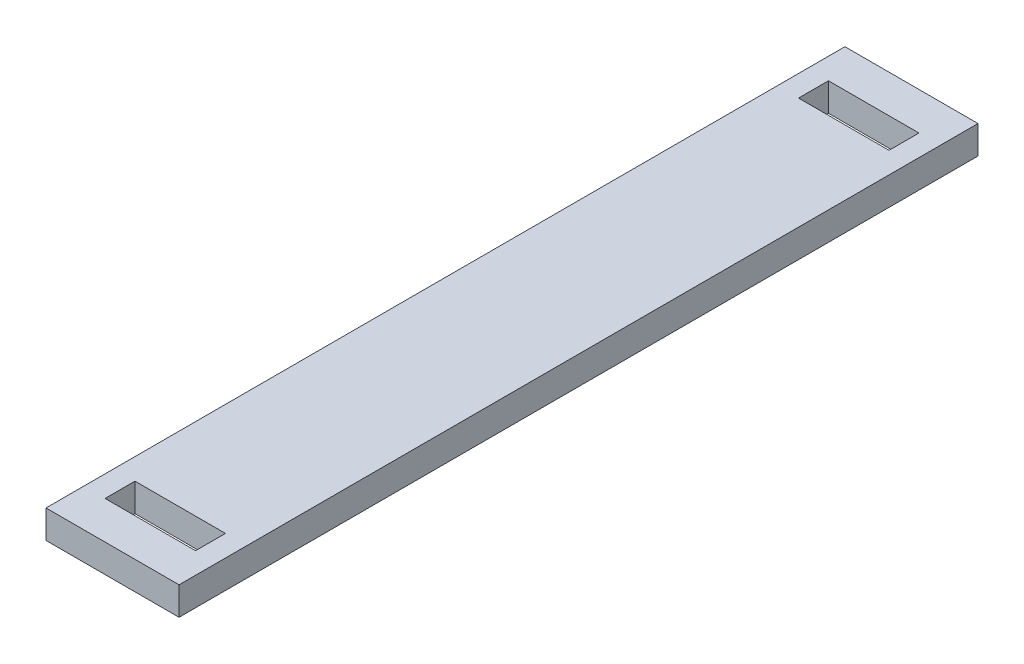
SolidWorks part; units mm, degrees
ref_plane "Front Plane" through (0, 0, 0) normal (0, 0, 1) x (1, 0, 0)
ref_plane "Top Plane" through (0, 0, 0) normal (0, 1, 0) x (1, 0, 0)
ref_plane "Right Plane" through (0, 0, 0) normal (1, 0, 0) x (0, 0, -1)
sketch "Sketch1" plane through (0, 0, 0) normal (0, 1, 0) x (1, 0, 0)
  line L1 (-15, -90.0622) -> (15, -90.0622)
  line L2 (-15, -90.0622) -> (-15, 90.0622)
  line L3 (-15, 90.0622) -> (15, 90.0622)
  line L4 (15, -90.0622) -> (15, 90.0622)
  line L5 (-15, -90.0622) -> (15, 90.0622) construction
  line L6 (-15, 90.0622) -> (15, -90.0622) construction
  point P0 (0, 0)
  dimension "D1" = 30
  dimension "D2" = 180.1244
extrude "Boss-Extrude1" add sketch "Sketch1" along normal blind 6.35 contours L2 L3 L4 L1
sketch "Sketch2" plane through (0, 6.35, 0) normal (0, 1, 0) x (1, 0, 0)
  line L0 (0, 78.175) -> (0, -78.175) construction
  line L1 (-10.2, 81.55) -> (10.2, 81.55)
  line L2 (-10.2, 81.55) -> (-10.2, 74.8)
  line L3 (-10.2, 74.8) -> (10.2, 74.8)
  line L4 (10.2, 81.55) -> (10.2, 74.8)
  line L5 (-10.2, 81.55) -> (10.2, 74.8) construction
  line L6 (-10.2, 74.8) -> (10.2, 81.55) construction
  line L7 (-10.2, -74.8) -> (10.2, -74.8)
  line L8 (-10.2, -74.8) -> (-10.2, -81.55)
  line L9 (-10.2, -81.55) -> (10.2, -81.55)
  line L10 (10.2, -74.8) -> (10.2, -81.55)
  line L11 (-10.2, -74.8) -> (10.2, -81.55) construction
  line L12 (-10.2, -81.55) -> (10.2, -74.8) construction
  point P0 (0, 78.175)
  point P5 (0, -78.175)
  point P10 (0, 0)
  dimension "D1" = 20.4
  dimension "D2" = 6.75
  dimension "D3" = 156.35
extrude "Cut-Extrude1" cut sketch "Sketch2" against normal blind 6.35
